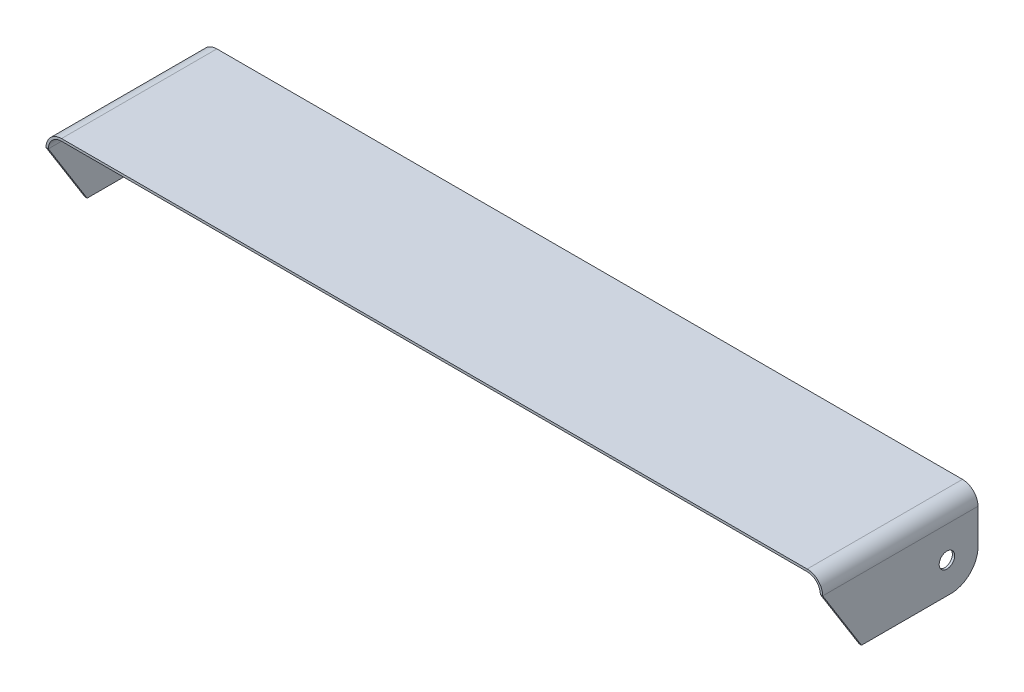
SolidWorks part; units mm, degrees
ref_plane "Front Plane" through (0, 0, 0) normal (0, 0, 1) x (1, 0, 0)
ref_plane "Top Plane" through (0, 0, 0) normal (0, 1, 0) x (1, 0, 0)
ref_plane "Right Plane" through (0, 0, 0) normal (1, 0, 0) x (0, 0, -1)
sketch "Sketch1" plane through (0, 0, 0) normal (0, 0, 1) x (1, 0, 0)
  line L0 (-500, 0) -> (-500, 80)
  line L1 (-480, 100) -> (480, 100)
  line L2 (500, 80) -> (500, 0)
  line L3 (-497, 0) -> (-497, 80)
  line L4 (-480, 97) -> (480, 97)
  line L5 (497, 80) -> (497, 0)
  line L6 (-500, 0) -> (-497, 0)
  line L7 (497, 0) -> (500, 0)
  arc A0 (480, 100) -> (500, 80) centre (480, 80) cw
  arc A1 (-500, 80) -> (-480, 100) centre (-480, 80) cw
  arc A2 (-497, 80) -> (-480, 97) centre (-480, 80) cw
  arc A3 (480, 97) -> (497, 80) centre (480, 80) cw
  point P8 (500, 100)
  point P11 (-500, 100)
  dimension "D4" = 20
  dimension "D1" = 1000
  dimension "D2" = 100
  dimension "D3" = 500
  dimension "D5" = 3
extrude "Boss-Extrude1" add sketch "Sketch1" along normal mid plane 200
sketch "Sketch2" plane through (500, 0, 0) normal (1, 0, 0) x (0, 0, -1)
  line L0 (-100, 80) -> (-100, 0)
  line L1 (-100, 0) -> (-100, 80) construction
  line L2 (-100, 0) -> (-50, 0)
  line L3 (-100, 0) -> (100, 0) construction
  line L4 (-50, 0) -> (-100, 80)
  dimension "D1" = 80
  dimension "D2" = 50
extrude "Cut-Extrude1" cut sketch "Sketch2" against normal through all
sketch "Sketch3" plane through (500, 0, 0) normal (1, 0, 0) x (0, 0, -1)
  line L0 (-100, 100) -> (100, 100) construction
  line L1 (100, 0) -> (100, 80) construction
  circle A0 centre (60, 40) radius 10
  dimension "D1" = 60
  dimension "D2" = 40
  dimension "D3" = 20
extrude "Cut-Extrude2" cut sketch "Sketch3" against normal through all
fillet "Fillet1" radius 35 2 edges at (-498.5, 0, -100) (498.5, 0, -100)
